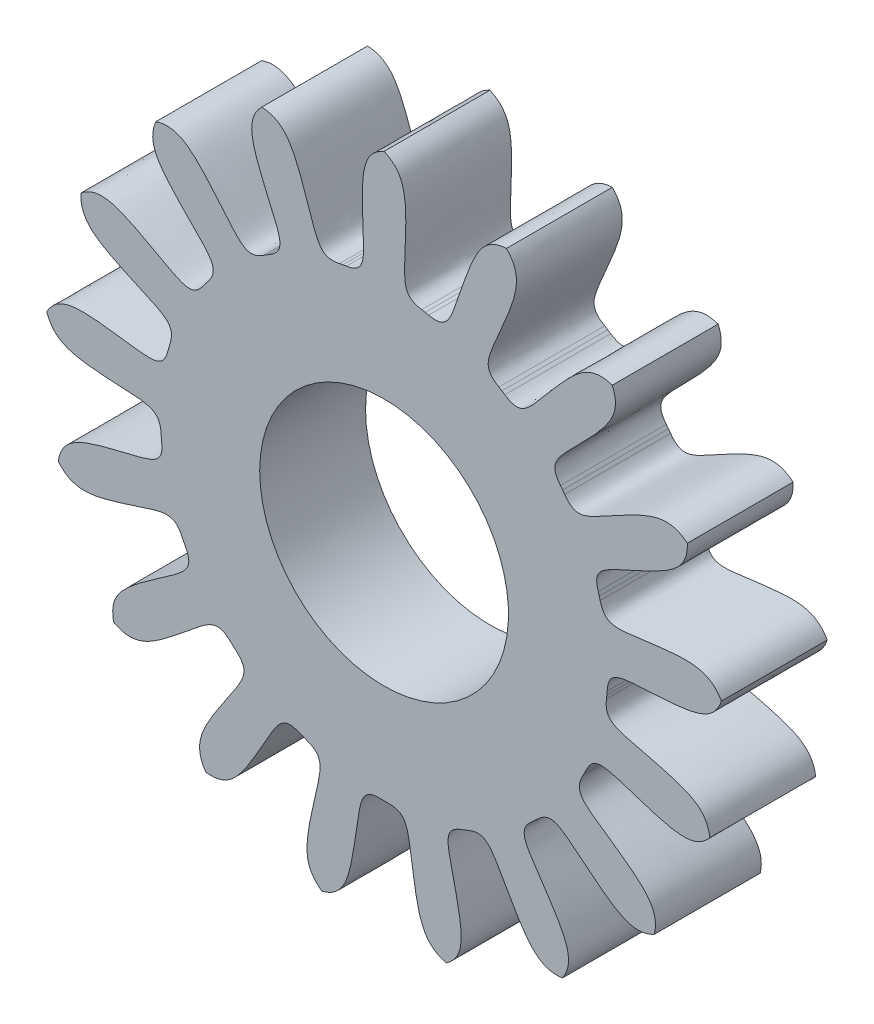
SolidWorks part; units mm, degrees
ref_plane "Alzado" through (0, 0, 0) normal (0, 0, 1) x (1, 0, 0)
ref_plane "Planta" through (0, 0, 0) normal (0, 1, 0) x (1, 0, 0)
ref_plane "Vista lateral" through (0, 0, 0) normal (1, 0, 0) x (0, 0, -1)
sketch "Sketch1" plane through (0, 0, 0) normal (0, 0, 1) x (1, 0, 0)
  line L0 (0, -1000) -> (0, 49000) construction
  line L1 (0, 0) -> (0.6543, 3.5) construction
  line L2 (0.2133, 1.2499) -> (0.233, 1.2464)
  line L3 (-0.2133, 1.2499) -> (-0.233, 1.2464)
  line L4 (0.2526, 1.2426) -> (0.233, 1.2464)
  line L5 (0.6504, 1.0885) -> (0.6675, 1.0781)
  line L6 (0.6844, 1.0674) -> (0.6675, 1.0781)
  line L7 (0.9997, 0.78) -> (1.0119, 0.7641)
  line L8 (1.0238, 0.7481) -> (1.0119, 0.7641)
  line L9 (1.214, 0.3662) -> (1.2196, 0.347)
  line L10 (1.2249, 0.3277) -> (1.2196, 0.347)
  line L11 (1.2643, -0.0971) -> (1.2626, -0.117)
  line L12 (1.2606, -0.1369) -> (1.2626, -0.117)
  line L13 (1.1438, -0.5472) -> (1.1351, -0.5652)
  line L14 (1.126, -0.583) -> (1.1351, -0.5652)
  line L15 (0.8689, -0.9235) -> (0.8542, -0.9371)
  line L16 (0.8394, -0.9504) -> (0.8542, -0.9371)
  line L17 (0.4766, -1.175) -> (0.4581, -1.1824)
  line L18 (0.4393, -1.1895) -> (0.4581, -1.1824)
  line L19 (0.02, -1.2678) -> (0, -1.268)
  line L20 (-0.02, -1.2678) -> (0, -1.268)
  line L21 (-0.4393, -1.1895) -> (-0.4581, -1.1824)
  line L22 (-0.4766, -1.175) -> (-0.4581, -1.1824)
  line L23 (-0.8394, -0.9504) -> (-0.8542, -0.9371)
  line L24 (-0.8689, -0.9235) -> (-0.8542, -0.9371)
  line L25 (-1.126, -0.583) -> (-1.1351, -0.5652)
  line L26 (-1.1438, -0.5472) -> (-1.1351, -0.5652)
  line L27 (-1.2606, -0.1369) -> (-1.2626, -0.117)
  line L28 (-1.2643, -0.0971) -> (-1.2626, -0.117)
  line L29 (-1.2249, 0.3277) -> (-1.2196, 0.347)
  line L30 (-1.214, 0.3662) -> (-1.2196, 0.347)
  line L31 (-1.0238, 0.7481) -> (-1.0119, 0.7641)
  line L32 (-0.9997, 0.78) -> (-1.0119, 0.7641)
  line L33 (-0.6844, 1.0674) -> (-0.6675, 1.0781)
  line L34 (-0.6504, 1.0885) -> (-0.6675, 1.0781)
  line L35 (-0.2526, 1.2426) -> (-0.233, 1.2464)
  circle A0 centre (0, 0) radius 1.92 construction
  circle A1 centre (0, 0) radius 1.268 construction
  spline S0 degree 3 poles (0, 1.92) (0.1051, 1.8729) (0.1297, 1.764) (0.1133, 1.3379) (0.1067, 1.2671) (0.2133, 1.2499) knots 0 0 0 0 0.42728 0.52728 1 1 1 1
  spline S1 degree 3 poles (0, 1.92) (-0.1051, 1.8729) (-0.1297, 1.764) (-0.1133, 1.3379) (-0.1067, 1.2671) (-0.2133, 1.2499) knots 0 0 0 0 0.42728 0.52728 1 1 1 1
  spline S2 degree 3 poles (0.6936, 1.7903) (0.5786, 1.7844) (0.5163, 1.6917) (0.3776, 1.2885) (0.3583, 1.2201) (0.2526, 1.2426) knots 0 0 0 0 0.42728 0.52728 1 1 1 1
  spline S3 degree 3 poles (0.6936, 1.7903) (0.7746, 1.7084) (0.7581, 1.598) (0.589, 1.2066) (0.5572, 1.143) (0.6504, 1.0885) knots 0 0 0 0 0.42728 0.52728 1 1 1 1
  spline S4 degree 3 poles (1.2935, 1.4189) (1.1841, 1.4549) (1.0926, 1.391) (0.8175, 1.065) (0.7748, 1.0083) (0.6844, 1.0674) knots 0 0 0 0 0.42728 0.52728 1 1 1 1
  spline S5 degree 3 poles (1.2935, 1.4189) (1.3394, 1.3133) (1.2842, 1.2163) (0.9851, 0.9123) (0.9325, 0.8646) (0.9997, 0.78) knots 0 0 0 0 0.42728 0.52728 1 1 1 1
  spline S6 degree 3 poles (1.7187, 0.8558) (1.6297, 0.9289) (1.5213, 0.9023) (1.1471, 0.6978) (1.0867, 0.6603) (1.0238, 0.7481) knots 0 0 0 0 0.42728 0.52728 1 1 1 1
  spline S7 degree 3 poles (1.7187, 0.8558) (1.7234, 0.7407) (1.6369, 0.6702) (1.2481, 0.4949) (1.1819, 0.4693) (1.214, 0.3662) knots 0 0 0 0 0.42728 0.52728 1 1 1 1
  spline S8 degree 3 poles (1.9118, 0.1772) (1.8552, 0.2775) (1.7445, 0.2919) (1.3217, 0.2363) (1.2519, 0.2232) (1.2249, 0.3277) knots 0 0 0 0 0.42728 0.52728 1 1 1 1
  spline S9 degree 3 poles (1.9118, 0.1772) (1.8746, 0.0682) (1.7684, 0.0337) (1.3426, 0.0106) (1.2716, 0.0107) (1.2643, -0.0971) knots 0 0 0 0 0.42728 0.52728 1 1 1 1
  spline S10 degree 3 poles (1.8467, -0.5254) (1.8301, -0.4115) (1.7321, -0.358) (1.3178, -0.2571) (1.248, -0.2441) (1.2606, -0.1369) knots 0 0 0 0 0.42728 0.52728 1 1 1 1
  spline S11 degree 3 poles (1.8467, -0.5254) (1.7726, -0.6136) (1.6612, -0.6074) (1.2558, -0.4751) (1.1896, -0.4494) (1.1438, -0.5472) knots 0 0 0 0 0.42728 0.52728 1 1 1 1
  spline S12 degree 3 poles (1.5322, -1.1571) (1.5579, -1.0448) (1.4858, -0.9596) (1.1359, -0.7158) (1.0755, -0.6785) (1.126, -0.583) knots 0 0 0 0 0.42728 0.52728 1 1 1 1
  spline S13 degree 3 poles (1.5322, -1.1571) (1.4312, -1.2125) (1.3296, -1.1665) (0.9993, -0.8967) (0.9469, -0.8488) (0.8689, -0.9235) knots 0 0 0 0 0.42728 0.52728 1 1 1 1
  spline S14 degree 3 poles (1.0107, -1.6324) (1.0753, -1.537) (1.0389, -1.4315) (0.8007, -1.0778) (0.7578, -1.0212) (0.8394, -0.9504) knots 0 0 0 0 0.42728 0.52728 1 1 1 1
  spline S15 degree 3 poles (1.0107, -1.6324) (0.8966, -1.6477) (0.8184, -1.568) (0.6079, -1.1971) (0.5764, -1.1335) (0.4766, -1.175) knots 0 0 0 0 0.42728 0.52728 1 1 1 1
  spline S16 degree 3 poles (0.3528, -1.8873) (0.4474, -1.8217) (0.4516, -1.7101) (0.3572, -1.2942) (0.3377, -1.226) (0.4393, -1.1895) knots 0 0 0 0 0.42728 0.52728 1 1 1 1
  spline S17 degree 3 poles (0.3528, -1.8873) (0.2408, -1.8603) (0.1967, -1.7578) (0.1344, -1.3359) (0.128, -1.2652) (0.02, -1.2678) knots 0 0 0 0 0.42728 0.52728 1 1 1 1
  spline S18 degree 3 poles (-0.3528, -1.8873) (-0.2408, -1.8603) (-0.1967, -1.7578) (-0.1344, -1.3359) (-0.128, -1.2652) (-0.02, -1.2678) knots 0 0 0 0 0.42728 0.52728 1 1 1 1
  spline S19 degree 3 poles (-0.3528, -1.8873) (-0.4474, -1.8217) (-0.4516, -1.7101) (-0.3572, -1.2942) (-0.3377, -1.226) (-0.4393, -1.1895) knots 0 0 0 0 0.42728 0.52728 1 1 1 1
  spline S20 degree 3 poles (-1.0107, -1.6324) (-0.8966, -1.6477) (-0.8184, -1.568) (-0.6079, -1.1971) (-0.5764, -1.1335) (-0.4766, -1.175) knots 0 0 0 0 0.42728 0.52728 1 1 1 1
  spline S21 degree 3 poles (-1.0107, -1.6324) (-1.0753, -1.537) (-1.0389, -1.4315) (-0.8007, -1.0778) (-0.7578, -1.0212) (-0.8394, -0.9504) knots 0 0 0 0 0.42728 0.52728 1 1 1 1
  spline S22 degree 3 poles (-1.5322, -1.1571) (-1.4312, -1.2125) (-1.3296, -1.1665) (-0.9993, -0.8967) (-0.9469, -0.8488) (-0.8689, -0.9235) knots 0 0 0 0 0.42728 0.52728 1 1 1 1
  spline S23 degree 3 poles (-1.5322, -1.1571) (-1.5579, -1.0448) (-1.4858, -0.9596) (-1.1359, -0.7158) (-1.0755, -0.6785) (-1.126, -0.583) knots 0 0 0 0 0.42728 0.52728 1 1 1 1
  spline S24 degree 3 poles (-1.8467, -0.5254) (-1.7726, -0.6136) (-1.6612, -0.6074) (-1.2558, -0.4751) (-1.1896, -0.4494) (-1.1438, -0.5472) knots 0 0 0 0 0.42728 0.52728 1 1 1 1
  spline S25 degree 3 poles (-1.8467, -0.5254) (-1.8301, -0.4115) (-1.7321, -0.358) (-1.3178, -0.2571) (-1.248, -0.2441) (-1.2606, -0.1369) knots 0 0 0 0 0.42728 0.52728 1 1 1 1
  spline S26 degree 3 poles (-1.9118, 0.1772) (-1.8746, 0.0682) (-1.7684, 0.0337) (-1.3426, 0.0106) (-1.2716, 0.0107) (-1.2643, -0.0971) knots 0 0 0 0 0.42728 0.52728 1 1 1 1
  spline S27 degree 3 poles (-1.9118, 0.1772) (-1.8552, 0.2775) (-1.7445, 0.2919) (-1.3217, 0.2363) (-1.2519, 0.2232) (-1.2249, 0.3277) knots 0 0 0 0 0.42728 0.52728 1 1 1 1
  spline S28 degree 3 poles (-1.7187, 0.8558) (-1.7234, 0.7407) (-1.6369, 0.6702) (-1.2481, 0.4949) (-1.1819, 0.4693) (-1.214, 0.3662) knots 0 0 0 0 0.42728 0.52728 1 1 1 1
  spline S29 degree 3 poles (-1.7187, 0.8558) (-1.6297, 0.9289) (-1.5213, 0.9023) (-1.1471, 0.6978) (-1.0867, 0.6603) (-1.0238, 0.7481) knots 0 0 0 0 0.42728 0.52728 1 1 1 1
  spline S30 degree 3 poles (-1.2935, 1.4189) (-1.3394, 1.3133) (-1.2842, 1.2163) (-0.9851, 0.9123) (-0.9325, 0.8646) (-0.9997, 0.78) knots 0 0 0 0 0.42728 0.52728 1 1 1 1
  spline S31 degree 3 poles (-1.2935, 1.4189) (-1.1841, 1.4549) (-1.0926, 1.391) (-0.8175, 1.065) (-0.7748, 1.0083) (-0.6844, 1.0674) knots 0 0 0 0 0.42728 0.52728 1 1 1 1
  spline S32 degree 3 poles (-0.6936, 1.7903) (-0.7746, 1.7084) (-0.7581, 1.598) (-0.589, 1.2066) (-0.5572, 1.143) (-0.6504, 1.0885) knots 0 0 0 0 0.42728 0.52728 1 1 1 1
  spline S33 degree 3 poles (-0.6936, 1.7903) (-0.5786, 1.7844) (-0.5163, 1.6917) (-0.3776, 1.2885) (-0.3583, 1.2201) (-0.2526, 1.2426) knots 0 0 0 0 0.42728 0.52728 1 1 1 1
  point P4 (0, 1.92)
  point P8 (0.233, 1.2464)
  point P9 (0.2133, 1.2499)
  point P132 (0, 0)
  dimension "D1" = 3.84
  dimension "D2" = 2.536
  dimension "D3" = 10.588
  dimension "D4" = 0.02
  dimension "D5" = 17
extrude "Boss-Extrude1 (17 teeth)" add sketch "Sketch1" along normal blind 0.6
sketch "Sketch2" plane through (0, 0, 0) normal (0, 0, 1) x (1, 0, 0)
  circle A0 centre (0, 0) radius 0.705
  dimension "D1" = 1.41
extrude "Cut-Extrude1" cut sketch "Sketch2" along normal up to next
